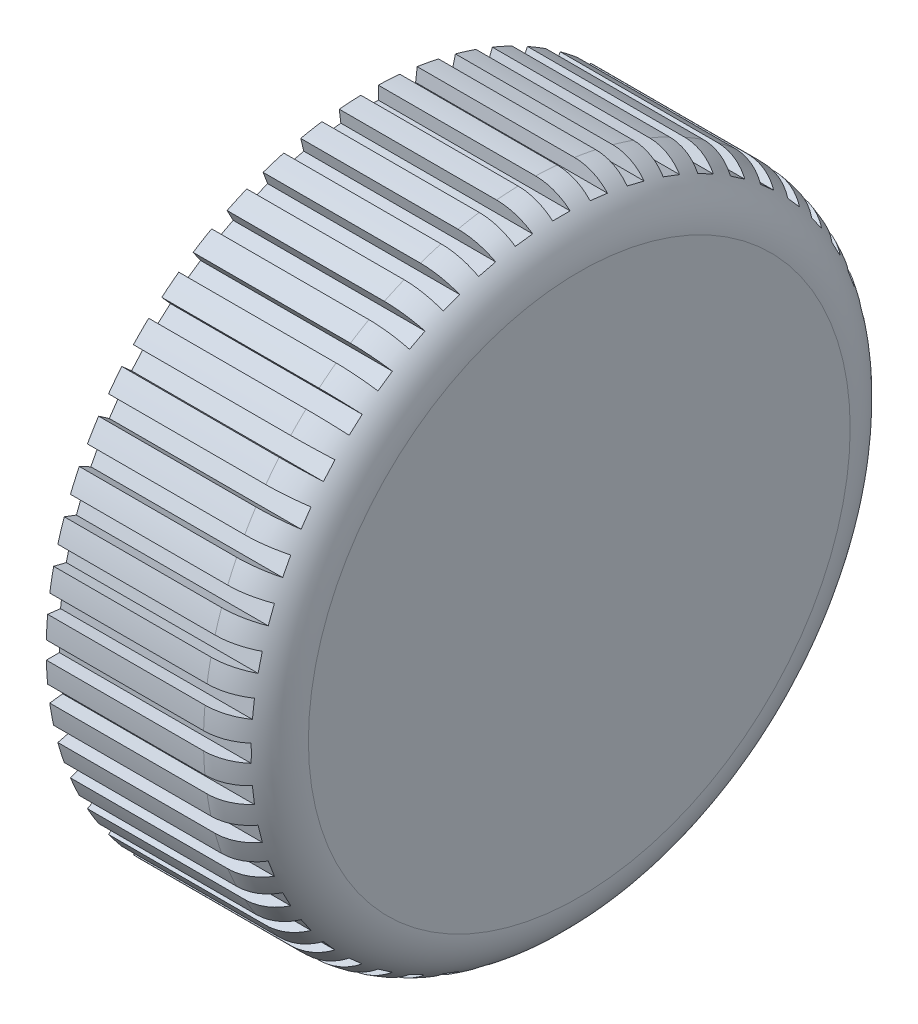
SolidWorks part; units mm, degrees
ref_plane "Спереди" through (0, 0, 0) normal (0, 0, 1) x (1, 0, 0)
ref_plane "Сверху" through (0, 0, 0) normal (0, 1, 0) x (1, 0, 0)
ref_plane "Справа" through (0, 0, 0) normal (1, 0, 0) x (0, 0, -1)
sketch "Эскиз1" plane through (0, 0, 0) normal (0, 0, 1) x (1, 0, 0)
  line L0 (0, 37) -> (0, 34.3)
  line L1 (0, 34.3) -> (16, 34.3)
  line L2 (16, 34.3) -> (16, 0)
  line L3 (16, 0) -> (24, 0)
  line L4 (24, 0) -> (24, 31)
  line L5 (18, 37) -> (0, 37)
  line L6 (0, 34.3) -> (0, 0) construction
  line L7 (0, 0) -> (16, 0) construction
  arc A0 (24, 31) -> (18, 37) centre (18, 31) ccw
  point P11 (16, 0)
  point P12 (16, 0.8507)
  dimension "D6" = 6
  dimension "D1" = 68.6
  dimension "D2" = 74
  dimension "D3" = 8
  dimension "D4" = 16
revolve "Повернуть1" add sketch "Эскиз1" angle 360 about L7
sketch "Эскиз2" plane through (0, 0, 0) normal (-1, 0, 0) x (0, 0, 1)
  line L0 (0, 35.5) -> (0, 0) construction
  line L1 (-1, 38.5) -> (1, 38.5)
  line L2 (-1, 38.5) -> (-1, 35.5)
  line L3 (-1, 35.5) -> (1, 35.5)
  line L4 (1, 38.5) -> (1, 35.5)
  line L5 (5.6334, 38.0988) -> (5.2718, 35.1206)
  line L6 (3.648, 38.3398) -> (3.2863, 35.3617)
  line L7 (3.648, 38.3398) -> (5.6334, 38.0988)
  line L8 (3.2863, 35.3617) -> (5.2718, 35.1206)
  line L9 (10.1846, 37.1419) -> (9.4666, 34.2291)
  line L10 (8.2427, 37.6206) -> (7.5248, 34.7078)
  line L11 (8.2427, 37.6206) -> (10.1846, 37.1419)
  line L12 (7.5248, 34.7078) -> (9.4666, 34.2291)
  line L13 (14.5873, 35.6435) -> (13.5235, 32.8385)
  line L14 (12.7173, 36.3527) -> (11.6535, 33.5477)
  line L15 (12.7173, 36.3527) -> (14.5873, 35.6435)
  line L16 (11.6535, 33.5477) -> (13.5235, 32.8385)
  line L17 (18.7773, 33.6253) -> (17.3831, 30.969)
  line L18 (17.0064, 34.5548) -> (15.6122, 31.8984)
  line L19 (17.0064, 34.5548) -> (18.7773, 33.6253)
  line L20 (15.6122, 31.8984) -> (17.3831, 30.969)
  line L21 (22.6935, 31.1168) -> (20.9893, 28.6479)
  line L22 (21.0475, 32.2529) -> (19.3433, 29.784)
  line L23 (21.0475, 32.2529) -> (22.6935, 31.1168)
  line L24 (19.3433, 29.784) -> (20.9893, 28.6479)
  line L25 (26.2787, 28.1545) -> (24.2894, 25.909)
  line L26 (24.7817, 29.4808) -> (22.7923, 27.2353)
  line L27 (24.7817, 29.4808) -> (26.2787, 28.1545)
  line L28 (22.7923, 27.2353) -> (24.2894, 25.909)
  line L29 (29.4808, 24.7817) -> (27.2353, 22.7923)
  line L30 (28.1545, 26.2787) -> (25.909, 24.2894)
  line L31 (28.1545, 26.2787) -> (29.4808, 24.7817)
  line L32 (25.909, 24.2894) -> (27.2353, 22.7923)
  line L33 (32.2529, 21.0475) -> (29.784, 19.3433)
  line L34 (31.1168, 22.6935) -> (28.6479, 20.9893)
  line L35 (31.1168, 22.6935) -> (32.2529, 21.0475)
  line L36 (28.6479, 20.9893) -> (29.784, 19.3433)
  line L37 (34.5548, 17.0064) -> (31.8984, 15.6122)
  line L38 (33.6253, 18.7773) -> (30.969, 17.3831)
  line L39 (33.6253, 18.7773) -> (34.5548, 17.0064)
  line L40 (30.969, 17.3831) -> (31.8984, 15.6122)
  line L41 (36.3527, 12.7173) -> (33.5477, 11.6535)
  line L42 (35.6435, 14.5873) -> (32.8385, 13.5235)
  line L43 (35.6435, 14.5873) -> (36.3527, 12.7173)
  line L44 (32.8385, 13.5235) -> (33.5477, 11.6535)
  line L45 (37.6206, 8.2427) -> (34.7078, 7.5248)
  line L46 (37.1419, 10.1846) -> (34.2291, 9.4666)
  line L47 (37.1419, 10.1846) -> (37.6206, 8.2427)
  line L48 (34.2291, 9.4666) -> (34.7078, 7.5248)
  line L49 (38.3398, 3.648) -> (35.3617, 3.2863)
  line L50 (38.0988, 5.6334) -> (35.1206, 5.2718)
  line L51 (38.0988, 5.6334) -> (38.3398, 3.648)
  line L52 (35.1206, 5.2718) -> (35.3617, 3.2863)
  line L53 (38.5, -1) -> (35.5, -1)
  line L54 (38.5, 1) -> (35.5, 1)
  line L55 (38.5, 1) -> (38.5, -1)
  line L56 (35.5, 1) -> (35.5, -1)
  line L57 (38.0988, -5.6334) -> (35.1206, -5.2718)
  line L58 (38.3398, -3.648) -> (35.3617, -3.2863)
  line L59 (38.3398, -3.648) -> (38.0988, -5.6334)
  line L60 (35.3617, -3.2863) -> (35.1206, -5.2718)
  line L61 (37.1419, -10.1846) -> (34.2291, -9.4666)
  line L62 (37.6206, -8.2427) -> (34.7078, -7.5248)
  line L63 (37.6206, -8.2427) -> (37.1419, -10.1846)
  line L64 (34.7078, -7.5248) -> (34.2291, -9.4666)
  line L65 (35.6435, -14.5873) -> (32.8385, -13.5235)
  line L66 (36.3527, -12.7173) -> (33.5477, -11.6535)
  line L67 (36.3527, -12.7173) -> (35.6435, -14.5873)
  line L68 (33.5477, -11.6535) -> (32.8385, -13.5235)
  line L69 (33.6253, -18.7773) -> (30.969, -17.3831)
  line L70 (34.5548, -17.0064) -> (31.8984, -15.6122)
  line L71 (34.5548, -17.0064) -> (33.6253, -18.7773)
  line L72 (31.8984, -15.6122) -> (30.969, -17.3831)
  line L73 (31.1168, -22.6935) -> (28.6479, -20.9893)
  line L74 (32.2529, -21.0475) -> (29.784, -19.3433)
  line L75 (32.2529, -21.0475) -> (31.1168, -22.6935)
  line L76 (29.784, -19.3433) -> (28.6479, -20.9893)
  line L77 (28.1545, -26.2787) -> (25.909, -24.2894)
  line L78 (29.4808, -24.7817) -> (27.2353, -22.7923)
  line L79 (29.4808, -24.7817) -> (28.1545, -26.2787)
  line L80 (27.2353, -22.7923) -> (25.909, -24.2894)
  line L81 (24.7817, -29.4808) -> (22.7923, -27.2353)
  line L82 (26.2787, -28.1545) -> (24.2894, -25.909)
  line L83 (26.2787, -28.1545) -> (24.7817, -29.4808)
  line L84 (24.2894, -25.909) -> (22.7923, -27.2353)
  line L85 (21.0475, -32.2529) -> (19.3433, -29.784)
  line L86 (22.6935, -31.1168) -> (20.9893, -28.6479)
  line L87 (22.6935, -31.1168) -> (21.0475, -32.2529)
  line L88 (20.9893, -28.6479) -> (19.3433, -29.784)
  line L89 (17.0064, -34.5548) -> (15.6122, -31.8984)
  line L90 (18.7773, -33.6253) -> (17.3831, -30.969)
  line L91 (18.7773, -33.6253) -> (17.0064, -34.5548)
  line L92 (17.3831, -30.969) -> (15.6122, -31.8984)
  line L93 (12.7173, -36.3527) -> (11.6535, -33.5477)
  line L94 (14.5873, -35.6435) -> (13.5235, -32.8385)
  line L95 (14.5873, -35.6435) -> (12.7173, -36.3527)
  line L96 (13.5235, -32.8385) -> (11.6535, -33.5477)
  line L97 (8.2427, -37.6206) -> (7.5248, -34.7078)
  line L98 (10.1846, -37.1419) -> (9.4666, -34.2291)
  line L99 (10.1846, -37.1419) -> (8.2427, -37.6206)
  line L100 (9.4666, -34.2291) -> (7.5248, -34.7078)
  line L101 (3.648, -38.3398) -> (3.2863, -35.3617)
  line L102 (5.6334, -38.0988) -> (5.2718, -35.1206)
  line L103 (5.6334, -38.0988) -> (3.648, -38.3398)
  line L104 (5.2718, -35.1206) -> (3.2863, -35.3617)
  line L105 (-1, -38.5) -> (-1, -35.5)
  line L106 (1, -38.5) -> (1, -35.5)
  line L107 (1, -38.5) -> (-1, -38.5)
  line L108 (1, -35.5) -> (-1, -35.5)
  line L109 (-5.6334, -38.0988) -> (-5.2718, -35.1206)
  line L110 (-3.648, -38.3398) -> (-3.2863, -35.3617)
  line L111 (-3.648, -38.3398) -> (-5.6334, -38.0988)
  line L112 (-3.2863, -35.3617) -> (-5.2718, -35.1206)
  line L113 (-10.1846, -37.1419) -> (-9.4666, -34.2291)
  line L114 (-8.2427, -37.6206) -> (-7.5248, -34.7078)
  line L115 (-8.2427, -37.6206) -> (-10.1846, -37.1419)
  line L116 (-7.5248, -34.7078) -> (-9.4666, -34.2291)
  line L117 (-14.5873, -35.6435) -> (-13.5235, -32.8385)
  line L118 (-12.7173, -36.3527) -> (-11.6535, -33.5477)
  line L119 (-12.7173, -36.3527) -> (-14.5873, -35.6435)
  line L120 (-11.6535, -33.5477) -> (-13.5235, -32.8385)
  line L121 (-18.7773, -33.6253) -> (-17.3831, -30.969)
  line L122 (-17.0064, -34.5548) -> (-15.6122, -31.8984)
  line L123 (-17.0064, -34.5548) -> (-18.7773, -33.6253)
  line L124 (-15.6122, -31.8984) -> (-17.3831, -30.969)
  line L125 (-22.6935, -31.1168) -> (-20.9893, -28.6479)
  line L126 (-21.0475, -32.2529) -> (-19.3433, -29.784)
  line L127 (-21.0475, -32.2529) -> (-22.6935, -31.1168)
  line L128 (-19.3433, -29.784) -> (-20.9893, -28.6479)
  line L129 (-26.2787, -28.1545) -> (-24.2894, -25.909)
  line L130 (-24.7817, -29.4808) -> (-22.7923, -27.2353)
  line L131 (-24.7817, -29.4808) -> (-26.2787, -28.1545)
  line L132 (-22.7923, -27.2353) -> (-24.2894, -25.909)
  line L133 (-29.4808, -24.7817) -> (-27.2353, -22.7923)
  line L134 (-28.1545, -26.2787) -> (-25.909, -24.2894)
  line L135 (-28.1545, -26.2787) -> (-29.4808, -24.7817)
  line L136 (-25.909, -24.2894) -> (-27.2353, -22.7923)
  line L137 (-32.2529, -21.0475) -> (-29.784, -19.3433)
  line L138 (-31.1168, -22.6935) -> (-28.6479, -20.9893)
  line L139 (-31.1168, -22.6935) -> (-32.2529, -21.0475)
  line L140 (-28.6479, -20.9893) -> (-29.784, -19.3433)
  line L141 (-34.5548, -17.0064) -> (-31.8984, -15.6122)
  line L142 (-33.6253, -18.7773) -> (-30.969, -17.3831)
  line L143 (-33.6253, -18.7773) -> (-34.5548, -17.0064)
  line L144 (-30.969, -17.3831) -> (-31.8984, -15.6122)
  line L145 (-36.3527, -12.7173) -> (-33.5477, -11.6535)
  line L146 (-35.6435, -14.5873) -> (-32.8385, -13.5235)
  line L147 (-35.6435, -14.5873) -> (-36.3527, -12.7173)
  line L148 (-32.8385, -13.5235) -> (-33.5477, -11.6535)
  line L149 (-37.6206, -8.2427) -> (-34.7078, -7.5248)
  line L150 (-37.1419, -10.1846) -> (-34.2291, -9.4666)
  line L151 (-37.1419, -10.1846) -> (-37.6206, -8.2427)
  line L152 (-34.2291, -9.4666) -> (-34.7078, -7.5248)
  line L153 (-38.3398, -3.648) -> (-35.3617, -3.2863)
  line L154 (-38.0988, -5.6334) -> (-35.1206, -5.2718)
  line L155 (-38.0988, -5.6334) -> (-38.3398, -3.648)
  line L156 (-35.1206, -5.2718) -> (-35.3617, -3.2863)
  line L157 (-38.5, 1) -> (-35.5, 1)
  line L158 (-38.5, -1) -> (-35.5, -1)
  line L159 (-38.5, -1) -> (-38.5, 1)
  line L160 (-35.5, -1) -> (-35.5, 1)
  line L161 (-38.0988, 5.6334) -> (-35.1206, 5.2718)
  line L162 (-38.3398, 3.648) -> (-35.3617, 3.2863)
  line L163 (-38.3398, 3.648) -> (-38.0988, 5.6334)
  line L164 (-35.3617, 3.2863) -> (-35.1206, 5.2718)
  line L165 (-37.1419, 10.1846) -> (-34.2291, 9.4666)
  line L166 (-37.6206, 8.2427) -> (-34.7078, 7.5248)
  line L167 (-37.6206, 8.2427) -> (-37.1419, 10.1846)
  line L168 (-34.7078, 7.5248) -> (-34.2291, 9.4666)
  line L169 (-35.6435, 14.5873) -> (-32.8385, 13.5235)
  line L170 (-36.3527, 12.7173) -> (-33.5477, 11.6535)
  line L171 (-36.3527, 12.7173) -> (-35.6435, 14.5873)
  line L172 (-33.5477, 11.6535) -> (-32.8385, 13.5235)
  line L173 (-33.6253, 18.7773) -> (-30.969, 17.3831)
  line L174 (-34.5548, 17.0064) -> (-31.8984, 15.6122)
  line L175 (-34.5548, 17.0064) -> (-33.6253, 18.7773)
  line L176 (-31.8984, 15.6122) -> (-30.969, 17.3831)
  line L177 (-31.1168, 22.6935) -> (-28.6479, 20.9893)
  line L178 (-32.2529, 21.0475) -> (-29.784, 19.3433)
  line L179 (-32.2529, 21.0475) -> (-31.1168, 22.6935)
  line L180 (-29.784, 19.3433) -> (-28.6479, 20.9893)
  line L181 (-28.1545, 26.2787) -> (-25.909, 24.2894)
  line L182 (-29.4808, 24.7817) -> (-27.2353, 22.7923)
  line L183 (-29.4808, 24.7817) -> (-28.1545, 26.2787)
  line L184 (-27.2353, 22.7923) -> (-25.909, 24.2894)
  line L185 (-24.7817, 29.4808) -> (-22.7923, 27.2353)
  line L186 (-26.2787, 28.1545) -> (-24.2894, 25.909)
  line L187 (-26.2787, 28.1545) -> (-24.7817, 29.4808)
  line L188 (-24.2894, 25.909) -> (-22.7923, 27.2353)
  line L189 (-21.0475, 32.2529) -> (-19.3433, 29.784)
  line L190 (-22.6935, 31.1168) -> (-20.9893, 28.6479)
  line L191 (-22.6935, 31.1168) -> (-21.0475, 32.2529)
  line L192 (-20.9893, 28.6479) -> (-19.3433, 29.784)
  line L193 (-17.0064, 34.5548) -> (-15.6122, 31.8984)
  line L194 (-18.7773, 33.6253) -> (-17.3831, 30.969)
  line L195 (-18.7773, 33.6253) -> (-17.0064, 34.5548)
  line L196 (-17.3831, 30.969) -> (-15.6122, 31.8984)
  line L197 (-12.7173, 36.3527) -> (-11.6535, 33.5477)
  line L198 (-14.5873, 35.6435) -> (-13.5235, 32.8385)
  line L199 (-14.5873, 35.6435) -> (-12.7173, 36.3527)
  line L200 (-13.5235, 32.8385) -> (-11.6535, 33.5477)
  line L201 (-8.2427, 37.6206) -> (-7.5248, 34.7078)
  line L202 (-10.1846, 37.1419) -> (-9.4666, 34.2291)
  line L203 (-10.1846, 37.1419) -> (-8.2427, 37.6206)
  line L204 (-9.4666, 34.2291) -> (-7.5248, 34.7078)
  line L205 (-3.648, 38.3398) -> (-3.2863, 35.3617)
  line L206 (-5.6334, 38.0988) -> (-5.2718, 35.1206)
  line L207 (-5.6334, 38.0988) -> (-3.648, 38.3398)
  line L208 (-5.2718, 35.1206) -> (-3.2863, 35.3617)
  point P213 (0, 0)
  dimension "D1" = 2
  dimension "D2" = 35.5
  dimension "D3" = 3
extrude "Вырез-Вытянуть2" cut sketch "Эскиз2" against normal through all
sketch "Эскиз3" plane through (0, 0, 0) normal (0, 0, 1) x (1, 0, 0)
  line L0 (0, 34.3) -> (0, -34.3) construction
  circle A0 centre (7, 0) radius 2.75
  dimension "D2" = 5.5
  dimension "D1" = 7
extrude "Бобышка-Вытянуть1" add sketch "Эскиз3" along normal up to next and the other way up to next
sketch "Эскиз4" plane through (0, 0, 0) normal (0, 0, 1) x (1, 0, 0)
  circle A0 centre (7, 0) radius 6.4741
extrude "Вырез-Вытянуть3" cut sketch "Эскиз4" against normal blind 33 and the other way blind 33
